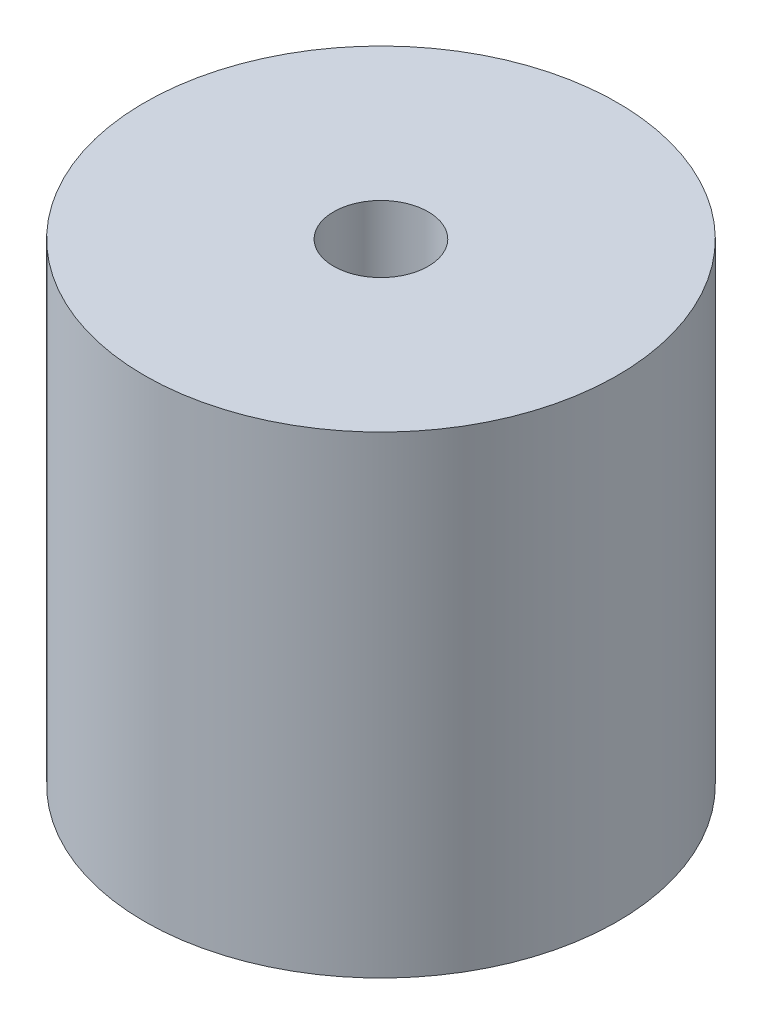
SolidWorks part; units mm, degrees
ref_plane "Front Plane" through (0, 0, 0) normal (0, 0, 1) x (1, 0, 0)
ref_plane "Top Plane" through (0, 0, 0) normal (0, 1, 0) x (1, 0, 0)
ref_plane "Right Plane" through (0, 0, 0) normal (1, 0, 0) x (0, 0, -1)
sketch "Sketch1" plane through (0, 0, 0) normal (0, 1, 0) x (1, 0, 0)
  circle A0 centre (0, 0) radius 10
  dimension "D1" = 20
extrude "Boss-Extrude1" add sketch "Sketch1" along normal blind 20
sketch "Sketch2" plane through (0, 20, 0) normal (0, 1, 0) x (1, 0, 0)
  circle A0 centre (0, 0) radius 2
extrude "Cut-Extrude1" cut sketch "Sketch2" against normal blind 10
